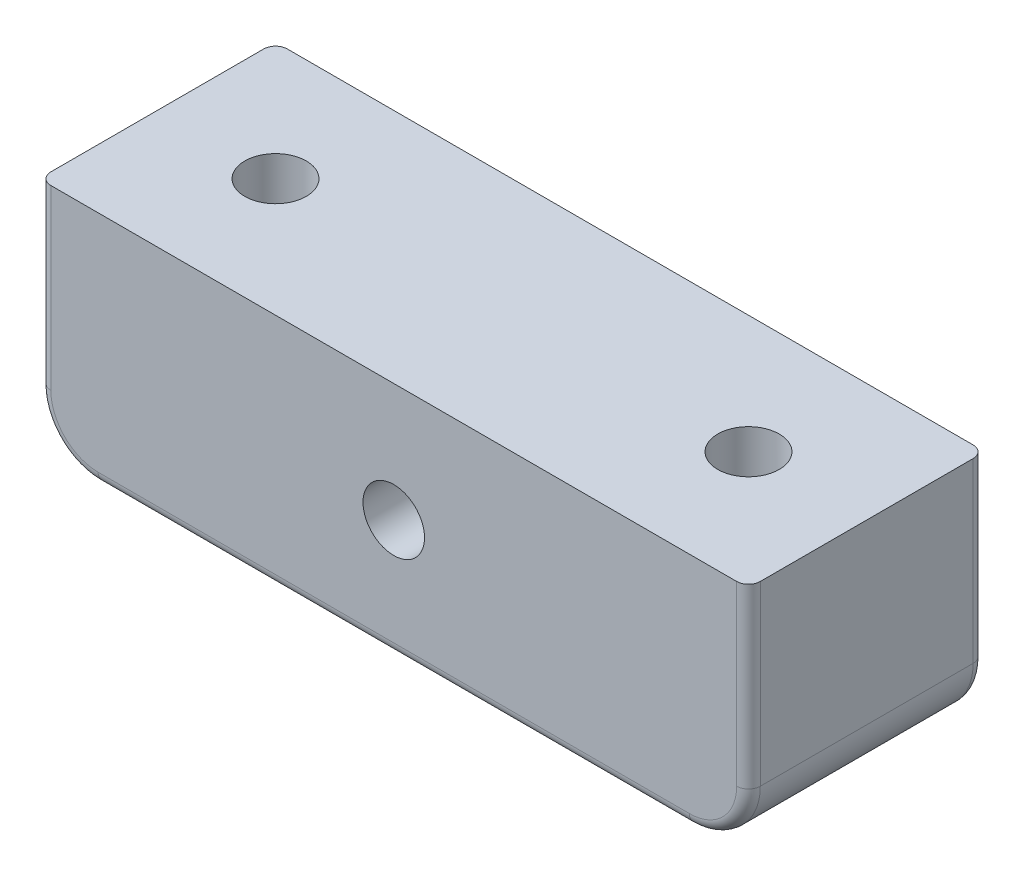
SolidWorks part; units mm, degrees
material "ABS"
ref_plane "Front Plane" through (0, 0, 0) normal (0, 0, 1) x (1, 0, 0)
ref_plane "Top Plane" through (0, 0, 0) normal (0, 1, 0) x (1, 0, 0)
ref_plane "Right Plane" through (0, 0, 0) normal (1, 0, 0) x (0, 0, -1)
sketch "Sketch1" plane through (0, 0, 0) normal (0, 0, 1) x (1, 0, 0)
  line L0 (0, 0) -> (0, -20) construction
  line L1 (-30, 0) -> (30, 0)
  line L2 (-30, 0) -> (-30, -15)
  line L3 (-25, -20) -> (25, -20)
  line L4 (30, 0) -> (30, -15)
  arc A0 (30, -15) -> (25, -20) centre (25, -15) cw
  arc A1 (-25, -20) -> (-30, -15) centre (-25, -15) cw
  circle A2 centre (0, -10) radius 2.6
  point P4 (0, 0)
  point P10 (-30, -20)
  dimension "D3" = 5
  dimension "D4" = 5.2
  dimension "D1" = 20
  dimension "D2" = 60
extrude "Boss-Extrude1" add sketch "Sketch1" along normal blind 20
sketch "Sketch2" plane through (0, 0, 0) normal (0, 1, 0) x (1, 0, 0)
  line L0 (0, 0) -> (0, -20) construction
  line L1 (30, 0) -> (-30, 0) construction
  line L2 (30, -20) -> (-30, -20) construction
  line L3 (0, -10) -> (-30, -10) construction
  line L4 (-30, -20) -> (-30, 0) construction
  circle A0 centre (-20, -10) radius 2.6
  circle A1 centre (20, -10) radius 2.6
  dimension "D1" = 5.2
  dimension "D2" = 20
extrude "Cut-Extrude1" cut sketch "Sketch2" against normal up to surface (20 mm away) up to face at (0, -20, 10)
sketch "Sketch3" plane through (0, 0, 0) normal (0, 0, -1) x (-1, 0, 0)
  line L1 (0, -17.5056) -> (6.5, -13.7528)
  line L2 (6.5, -13.7528) -> (6.5, -6.2472)
  line L3 (6.5, -6.2472) -> (0, -2.4944)
  line L4 (0, -2.4944) -> (-6.5, -6.2472)
  line L5 (-6.5, -6.2472) -> (-6.5, -13.7528)
  line L6 (-6.5, -13.7528) -> (0, -17.5056)
  line L7 (-30, 0) -> (30, 0) construction
  circle A0 centre (0, -10) radius 6.5 construction
  dimension "D1" = 13
extrude "Cut-Extrude2" cut sketch "Sketch3" against normal blind 3
fillet "Fillet1" radius 1 10 edges at (-30, -7.5, 0) (-28.5355, -18.5355, 0) (0, -20, 0) (30, -7.5, 0) (-30, -7.5, 20) (-28.5355, -18.5355, 20) (0, -20, 20) (30, -7.5, 20) (28.5355, -18.5355, 0) (28.5355, -18.5355, 20)
